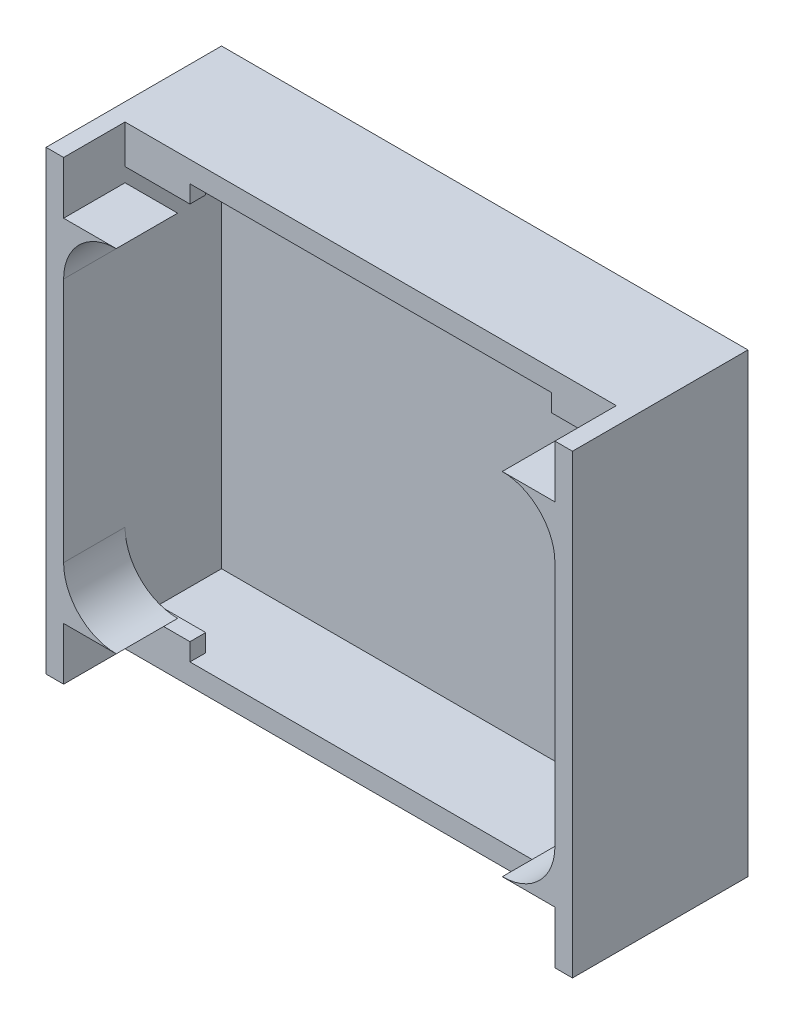
SolidWorks part; units mm, degrees
ref_plane "Ön Düzlem" through (0, 0, 0) normal (0, 0, 1) x (1, 0, 0)
ref_plane "Üst Düzlem" through (0, 0, 0) normal (0, 1, 0) x (1, 0, 0)
ref_plane "Sağ Düzlem" through (0, 0, 0) normal (1, 0, 0) x (0, 0, -1)
sketch "Sketch1" plane through (0, 0, 0) normal (0, 0, 1) x (1, 0, 0)
  line L1 (-14.7751, 15.219) -> (15.2249, 15.219)
  line L2 (-14.7751, 15.219) -> (-14.7751, -10.781)
  line L3 (-14.7751, -10.781) -> (15.2249, -10.781)
  line L4 (15.2249, 15.219) -> (15.2249, -10.781)
  dimension "D1" = 30
  dimension "D2" = 26
extrude "Boss-Extrude1" add sketch "Sketch1" along normal blind 10
sketch "Sketch2" plane through (0, 0, 10) normal (0, 0, 1) x (1, 0, 0)
  line L1 (-14.7751, 15.219) -> (-14.7751, -10.781) construction
  line L2 (-14.7751, -10.781) -> (15.2249, -10.781) construction
  line L3 (15.2249, 15.219) -> (-14.7751, 15.219) construction
  line L4 (15.2249, -10.781) -> (15.2249, 15.219) construction
  line L8 (-13.7751, 9.219) -> (-13.7751, -4.781)
  line L9 (14.2249, 9.219) -> (14.2249, -4.781)
  line L10 (-10.7751, 15.219) -> (11.2249, 15.219)
  line L11 (-10.7751, 12.219) -> (-10.7751, 15.219)
  line L15 (-10.7751, -10.781) -> (-10.7751, -7.781)
  line L17 (11.2249, 15.219) -> (11.2249, 12.219)
  line L18 (11.2249, -7.781) -> (11.2249, -10.781)
  line L19 (11.2249, -10.781) -> (-10.7751, -10.781)
  arc A0 (-13.7751, -4.781) -> (-10.7751, -7.781) centre (-10.7751, -4.781) ccw
  arc A1 (14.2249, 9.219) -> (11.2249, 12.219) centre (11.2249, 9.219) ccw
  arc A2 (-10.7751, 12.219) -> (-13.7751, 9.219) centre (-10.7751, 9.219) ccw
  arc A3 (11.2249, -7.781) -> (14.2249, -4.781) centre (11.2249, -4.781) ccw
  dimension "D1" = 4
  dimension "D3" = 6
  dimension "D2" = 6
  dimension "D4" = 4
extrude "Cut-Extrude2" cut sketch "Sketch2" against normal blind 3.5
sketch "Sketch3" plane through (0, 0, 10) normal (0, 0, 1) x (1, 0, 0)
  line L0 (-10.7751, 15.219) -> (-14.7751, 15.219) construction
  line L1 (-10.7751, 12.219) -> (-13.7751, 12.219)
  line L2 (-10.7751, 12.219) -> (-10.7751, 15.219)
  line L3 (-10.7751, 15.219) -> (-13.7751, 15.219)
  line L4 (-13.7751, 12.219) -> (-13.7751, 15.219)
  line L5 (11.2249, -10.781) -> (15.2249, -10.781) construction
  line L6 (11.2249, -7.781) -> (14.2249, -7.781)
  line L7 (11.2249, -7.781) -> (11.2249, -10.781)
  line L8 (11.2249, -10.781) -> (14.2249, -10.781)
  line L9 (14.2249, -7.781) -> (14.2249, -10.781)
  line L10 (15.2249, -10.781) -> (15.2249, 15.219) construction
  line L11 (-14.7751, -10.781) -> (-10.7751, -10.781) construction
  line L12 (-10.7751, -7.781) -> (-13.7751, -7.781)
  line L13 (-10.7751, -7.781) -> (-10.7751, -10.781)
  line L14 (-10.7751, -10.781) -> (-13.7751, -10.781)
  line L15 (-13.7751, -7.781) -> (-13.7751, -10.781)
  line L16 (15.2249, 15.219) -> (11.2249, 15.219) construction
  line L17 (11.2249, 12.219) -> (14.2249, 12.219)
  line L18 (11.2249, 12.219) -> (11.2249, 15.219)
  line L19 (11.2249, 15.219) -> (14.2249, 15.219)
  line L20 (14.2249, 12.219) -> (14.2249, 15.219)
  dimension "D1" = 1
  dimension "D2" = 1
extrude "Cut-Extrude3" cut sketch "Sketch3" against normal blind 3.5
sketch "Sketch4" plane through (0, 0, 6.5) normal (0, 0, 1) x (1, 0, 0)
  line L0 (14.2249, 15.219) -> (-13.7751, 15.219) construction
  line L1 (-13.7751, 14.019) -> (14.2249, 14.019)
  line L2 (-13.7751, 14.019) -> (-13.7751, -9.581)
  line L3 (-13.7751, -9.581) -> (14.2249, -9.581)
  line L4 (14.2249, 14.019) -> (14.2249, -9.581)
  line L5 (-13.7751, -10.781) -> (14.2249, -10.781) construction
  line L6 (15.2249, -10.781) -> (15.2249, 15.219) construction
  line L7 (-14.7751, 15.219) -> (-14.7751, -10.781) construction
  dimension "D1" = 1.2
  dimension "D2" = 1.2
  dimension "D3" = 1
  dimension "D4" = 1
extrude "Cut-Extrude4" cut sketch "Sketch4" against normal blind 5.5
sketch "Sketch5" plane through (0, 14.019, 0) normal (0, -1, 0) x (-1, 0, 0)
  line L0 (-14.2249, -6.5) -> (13.7751, -6.5) construction
  line L1 (13.7751, -6.5) -> (10.0751, -6.5)
  line L2 (13.7751, -6.5) -> (13.7751, -5.6)
  line L3 (13.7751, -5.6) -> (10.0751, -5.6)
  line L4 (10.0751, -6.5) -> (10.0751, -5.6)
  line L6 (-14.2249, -6.5) -> (-10.5249, -6.5)
  line L7 (-14.2249, -6.5) -> (-14.2249, -5.6)
  line L8 (-14.2249, -5.6) -> (-10.5249, -5.6)
  line L9 (-10.5249, -6.5) -> (-10.5249, -5.6)
  dimension "D1" = 0.9
  dimension "D2" = 0
  dimension "D3" = 3.7
  dimension "D4" = 3.7
extrude "Boss-Extrude2" add sketch "Sketch5" along normal blind 1
sketch "Sketch6" plane through (0, -9.581, 0) normal (0, 1, 0) x (1, 0, 0)
  line L1 (14.2249, -6.5) -> (10.5249, -6.5)
  line L2 (14.2249, -6.5) -> (14.2249, -5.6)
  line L3 (14.2249, -5.6) -> (10.5249, -5.6)
  line L4 (10.5249, -6.5) -> (10.5249, -5.6)
  line L5 (-13.7751, -6.5) -> (-10.0751, -6.5)
  line L6 (-13.7751, -6.5) -> (-13.7751, -5.6)
  line L7 (-13.7751, -5.6) -> (-10.0751, -5.6)
  line L8 (-10.0751, -6.5) -> (-10.0751, -5.6)
  dimension "D1" = 0.9
  dimension "D2" = 3.7
  dimension "D3" = 3.7
extrude "Boss-Extrude3" add sketch "Sketch6" along normal blind 1
